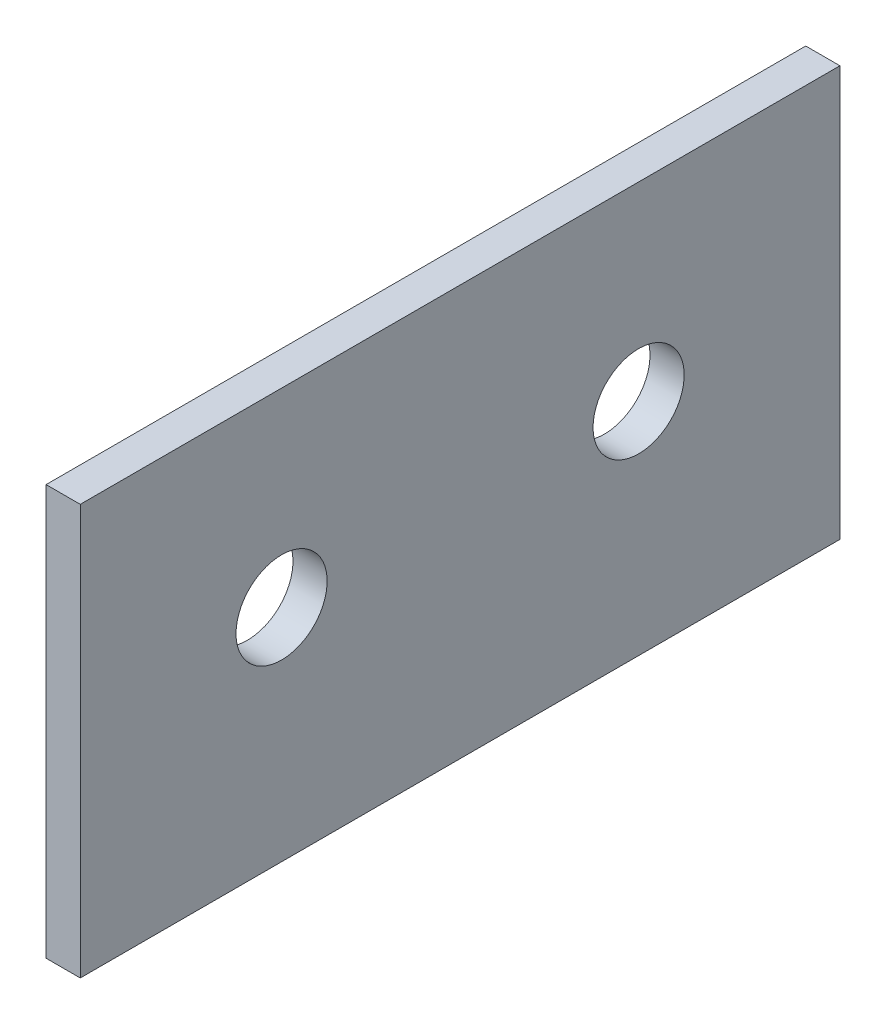
SolidWorks part; units mm, degrees
material "3003 Alaşım"
ref_plane "Ön Düzlem" through (0, 0, 0) normal (0, 0, 1) x (1, 0, 0)
ref_plane "Üst Düzlem" through (0, 0, 0) normal (0, 1, 0) x (1, 0, 0)
ref_plane "Sağ Düzlem" through (0, 0, 0) normal (1, 0, 0) x (0, 0, -1)
sketch "Çizim1" plane through (0, 0, 0) normal (0, 0, 1) x (1, 0, 0)
  line L0 (0, 0) -> (0, 29)
  line L1 (1, 30) -> (57, 30)
  line L2 (58, 29) -> (58, 0)
  arc A0 (0, 29) -> (1, 30) centre (1, 29) cw
  arc A1 (57, 30) -> (58, 29) centre (57, 29) cw
  point P7 (0, 30)
  point P10 (58, 30)
  dimension "D3" = 1
  dimension "D1" = 58
  dimension "D2" = 30
  dimension "D4" = 29
extrude "Ekstrüzyon-İnce1" add sketch "Çizim1" along normal blind 50 thin
sketch "Çizim2" plane through (58, 0, 0) normal (1, 0, 0) x (0, 0, -1)
  line L0 (-50, 14.5) -> (0, 14.5) construction
  line L1 (-50, 29) -> (-50, 0) construction
  line L2 (0, 29) -> (0, 0) construction
  line L3 (-25, 25.8154) -> (-25, 3.1846) construction
  line L4 (-36.75, 25.8154) -> (-36.75, 3.1846) construction
  line L5 (-13.25, 25.8154) -> (-13.25, 3.1846) construction
  circle A0 centre (-36.75, 14.5) radius 3
  circle A1 centre (-13.25, 14.5) radius 3
  point P9 (-25, 14.5)
  dimension "D1" = 11.75
  dimension "D2" = 11.75
extrude "Kes-Ekstrüzyon1" cut sketch "Çizim2" against normal blind 78
sketch "Çizim3" plane through (0, 0, 0) normal (-1, 0, 0) x (0, 0, 1)
  circle A0 centre (46.9263, 2.6362) radius 0.5
extrude "Kes-Ekstrüzyon2" cut sketch "Çizim3" against normal blind 22
sketch "Çizim4" plane through (0, 0, 0) normal (-1, 0, 0) x (0, 0, 1)
  circle A0 centre (36.75, 14.5) radius 6
extrude "Kes-Ekstrüzyon3" cut sketch "Çizim4" against normal blind 22
scale "Scale1" scale about centroid uniform scaling yes scale factor 0.666667
sketch "Sketch2" plane through (0, 26.7463, 0) normal (0, -1, 0) x (1, 0, 0)
  line L0 (-988.1219, 8.2728) -> (49011.8781, 8.2728) construction
  line L2 (-983.1335, 41.6061) -> (49016.8665, 41.6061) construction
  line L4 (10.4791, -979.5474) -> (10.4791, 49020.4526) construction
  line L6 (47.8124, -986.5623) -> (47.8124, 49013.4377) construction
sketch "Sketch3" plane through (48.4791, 0, 0) normal (1, 0, 0) x (0, 0, -1)
  line L0 (-41.6061, 7.4129) -> (-8.2728, 7.4129) construction
  line L1 (-41.6061, 26.7463) -> (-8.2728, 26.7463)
  line L2 (-41.6061, 26.7463) -> (-41.6061, 7.4129)
  line L3 (-41.6061, 7.4129) -> (-8.2728, 7.4129)
  line L4 (-8.2728, 26.7463) -> (-8.2728, 7.4129)
extrude "Cut-Extrude1" cut sketch "Sketch3" against normal blind 2
sketch "Sketch4" plane through (0, 27.4129, 0) normal (0, 1, 0) x (1, 0, 0)
  line L0 (10.4791, 200979.5474) -> (10.4791, -249020.4526) construction
  line L1 (10.4791, 2.5616) -> (66.4791, 2.5616)
  line L2 (10.4791, 2.5616) -> (10.4791, -52.4384)
  line L3 (10.4791, -52.4384) -> (66.4791, -52.4384)
  line L4 (66.4791, 2.5616) -> (66.4791, -52.4384)
  line L6 (-200988.1219, -8.2728) -> (249011.8781, -8.2728) construction
  line L7 (-200983.1335, -41.6061) -> (249016.8665, -41.6061) construction
  dimension "D1" = 56
  dimension "D2" = 55
  dimension "D3" = 10.8344
  dimension "D4" = 10.8323
extrude "Boss-Extrude1" add sketch "Sketch4" against normal blind 2
sketch "Sketch5" plane through (66.4791, 0, 0) normal (1, 0, 0) x (0, 0, -1)
  line L1 (-8.2728, 25.4129) -> (-41.6061, 25.4129)
  line L2 (-8.2728, 25.4129) -> (-8.2728, 7.4129)
  line L3 (-8.2728, 7.4129) -> (-41.6061, 7.4129)
  line L4 (-41.6061, 25.4129) -> (-41.6061, 7.4129)
extrude "Boss-Extrude2" add sketch "Sketch5" against normal blind 1.5
sketch "Sketch6" plane through (64.9791, 0, 0) normal (-1, 0, 0) x (0, 0, 1)
  circle A0 centre (17.1061, 17.0796) radius 2
  circle A1 centre (32.7728, 17.0796) radius 2
  circle A2 centre (32.7728, 17.0796) radius 4 construction
  dimension "D1" = 4
  dimension "D2" = 2
extrude "Cut-Extrude2" cut sketch "Sketch6" against normal blind 1.5
sketch "Sketch7" plane through (0, 0, -2.5616) normal (0, 0, -1) x (-1, 0, 0)
  line L13 (-64.9791, 7.4129) -> (-8.0148, 7.4129)
  line L14 (-64.9791, 7.4129) -> (-64.9791, 30.4471)
  line L15 (-64.9791, 30.4471) -> (-8.0148, 30.4471)
  line L16 (-8.0148, 7.4129) -> (-8.0148, 30.4471)
extrude "Cut-Extrude5" cut sketch "Sketch7" against normal through all
sketch "Sketch8" plane through (64.9791, 0, 0) normal (-1, 0, 0) x (0, 0, 1)
  line L1 (52.4384, 25.4129) -> (-3.704, 25.4129)
  line L2 (52.4384, 25.4129) -> (52.4384, 29.79)
  line L3 (52.4384, 29.79) -> (-3.704, 29.79)
  line L4 (-3.704, 25.4129) -> (-3.704, 29.79)
extrude "Cut-Extrude6" cut sketch "Sketch8" against normal through all
